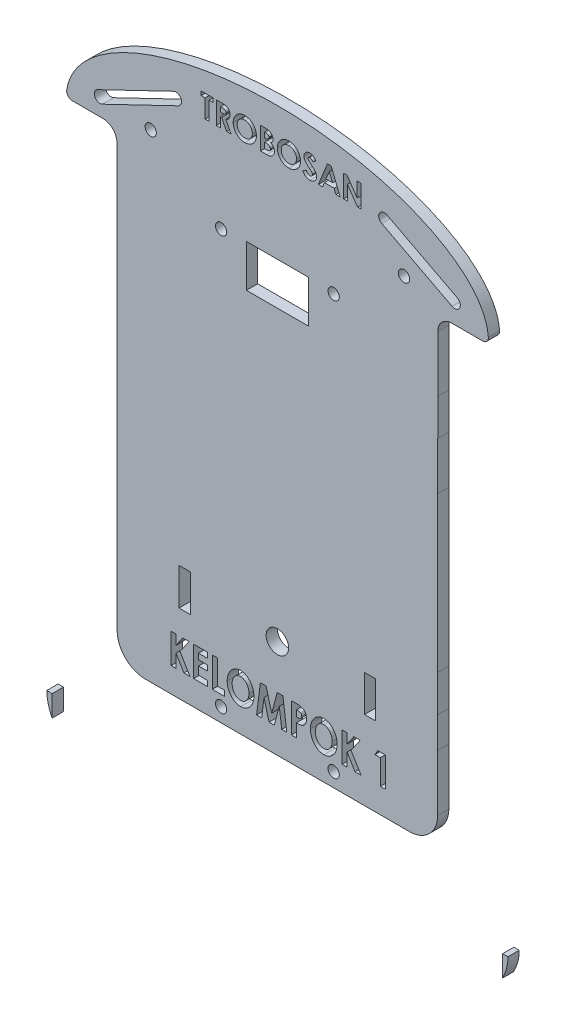
SolidWorks part; units mm, degrees
ref_plane "Front Plane" through (0, 0, 0) normal (0, 0, 1) x (1, 0, 0)
ref_plane "Top Plane" through (0, 0, 0) normal (0, 1, 0) x (1, 0, 0)
ref_plane "Right Plane" through (0, 0, 0) normal (1, 0, 0) x (0, 0, -1)
sketch "Sketch1" plane through (0, 0, 0) normal (0, 0, 1) x (1, 0, 0)
  line L0 (50.4961, 0) -> (-50.4961, 0) construction
  line L1 (0, 94) -> (0, -94) construction
  line L2 (-57, 93) -> (-57, 43.7851)
  line L3 (-56.98, 18) -> (-56.97, 18)
  line L4 (-56.97, 18) -> (-56.97, -18)
  line L5 (-56.97, -18) -> (-56.96, -18)
  line L6 (-56.96, -18) -> (-56.96, -31)
  line L8 (56.96, -18) -> (56.96, -31)
  line L9 (56.96, -18) -> (56.97, -18)
  line L10 (56.97, -18) -> (56.97, 37)
  line L11 (56.97, 37) -> (56.98, 37)
  line L12 (57, 92) -> (57, 67)
  line L13 (0, 94) -> (0, 138.6441) construction
  line L14 (-75, 93) -> (-57, 93)
  line L15 (57, 92) -> (74.9694, 92)
  line L16 (-81.94, -93) -> (-56.94, -93)
  line L17 (56.94, -93) -> (81.94, -93)
  line L18 (-57, 43.7851) -> (-56.99, 43.8393)
  line L19 (-56.99, 43.8393) -> (-56.99, 35)
  line L20 (-56.99, 35) -> (-56.98, 35)
  line L21 (-56.98, 35) -> (-56.98, 18)
  line L22 (57, 67) -> (56.99, 67)
  line L23 (56.99, 67) -> (56.99, 54)
  line L24 (56.99, 54) -> (56.98, 54)
  line L25 (56.98, 54) -> (56.98, 37)
  line L26 (-56.96, -31) -> (-56.95, -31)
  line L27 (-56.95, -42) -> (-56.94, -42)
  line L28 (-56.94, -42) -> (-56.94, -93)
  line L29 (-56.95, -31) -> (-56.95, -42)
  line L30 (-56.94, -93) -> (56.94, -93) construction
  line L31 (56.96, -31) -> (56.95, -31)
  line L32 (56.95, -31) -> (56.95, -42)
  line L33 (56.95, -42) -> (56.94, -42)
  line L34 (56.94, -42) -> (56.94, -93)
  circle A2 centre (0, 94) radius 10
  circle A3 centre (0, -94) radius 10
  circle A4 centre (0, 0) radius 1.9726
  ellipse E0 centre (0, 93) end of major axis (-75, 93) minor radius 35 (-75, 93) -> (74.9694, 92) cw
  ellipse E1 centre (0, -93) end of major axis (81.94, -93) minor radius 35 (-81.94, -93) -> (81.94, -93) ccw
  point P4 (0, 0)
  point P8 (0, 0)
  point P39 (0, -128)
  point P53 (-57, 93)
extrude "Boss-Extrude2" add sketch "Sketch1" along normal blind 4
sketch "Sketch25" plane through (0, 0, 0) normal (0, 0, -1) x (-1, 0, 0)
  line L1 (-30.9594, 48) -> (-30.9594, 34.3965) construction
  line L5 (-30.9594, 48) -> (-25.9623, 48)
  line L6 (-30.9594, 48) -> (-30.9594, 35.0074)
  line L7 (-30.9594, 35.0074) -> (-25.9623, 35.0074)
  line L8 (-25.9623, 48) -> (-25.9623, 35.0074)
  line L12 (25.0086, 48) -> (30.0057, 48)
  line L13 (25.0086, 48) -> (25.0086, 35.0074)
  line L14 (25.0086, 35.0074) -> (30.0057, 35.0074)
  line L15 (30.0057, 48) -> (30.0057, 35.0074)
  line L22 (-39.9543, -30.9549) -> (-34.9572, -30.9549)
  line L23 (-39.9543, -30.9549) -> (-39.9543, -43.9474)
  line L24 (-39.9543, -43.9474) -> (-34.9572, -43.9474)
  line L25 (-34.9572, -30.9549) -> (-34.9572, -43.9474)
  line L26 (35.0029, -30.9549) -> (40, -30.9549)
  line L27 (35.0029, -30.9549) -> (35.0029, -43.9474)
  line L28 (35.0029, -43.9474) -> (40, -43.9474)
  line L29 (40, -30.9549) -> (40, -43.9474)
  dimension "D2" = 4.9971
  dimension "D5" = 4.9971
  dimension "D7" = 4.9971
  dimension "D8" = 4.9971
extrude "Cut-Extrude25" cut sketch "Sketch25" against normal through all
sketch "Sketch28" plane through (0, 0, 0) normal (0, 0, -1) x (-1, 0, 0)
  line L1 (30, -112) -> (-30, -112)
  line L2 (-30, 112) -> (30, 112) construction
  line L3 (-30, 114) -> (30, 114)
  line L4 (-30, 110) -> (30, 110)
  line L5 (-30, -112) -> (30, -112) construction
  line L6 (-30, -110) -> (30, -110)
  line L7 (-30, -114) -> (30, -114)
  line L8 (-63, 99) -> (-38, 112) construction
  line L9 (-63.9227, 100.7744) -> (-38.9227, 113.7744)
  line L10 (-62.0773, 97.2256) -> (-37.0773, 110.2256)
  line L11 (36.0632, 112.09) -> (63.0485, 99.1007) construction
  line L12 (36.9306, 113.8921) -> (63.9159, 100.9028)
  line L13 (35.1957, 110.2879) -> (62.1811, 97.2986)
  line L21 (36, -112) -> (63, -99) construction
  line L22 (35.1324, -110.198) -> (62.1324, -97.198)
  line L23 (36.8676, -113.802) -> (63.8676, -100.802)
  line L24 (-63, -99) -> (-38, -112.1208) construction
  line L25 (-62.0706, -97.2291) -> (-37.0706, -110.3499)
  line L26 (-63.9294, -100.7709) -> (-38.9294, -113.8918)
  arc A0 (-30, 114) -> (-30, 110) centre (-30, 112) ccw
  arc A1 (30, 110) -> (30, 114) centre (30, 112) ccw
  arc A2 (-63.9227, 100.7744) -> (-62.0773, 97.2256) centre (-63, 99) ccw
  arc A4 (-37.0773, 110.2256) -> (-38.9227, 113.7744) centre (-38, 112) ccw
  arc A5 (36.9306, 113.8921) -> (35.1957, 110.2879) centre (36.0632, 112.09) ccw
  arc A6 (62.1811, 97.2986) -> (63.9159, 100.9028) centre (63.0485, 99.1007) ccw
  arc A7 (35.1324, -110.198) -> (36.8676, -113.802) centre (36, -112) ccw
  arc A8 (-30, -110) -> (-30, -114) centre (-30, -112) ccw
  arc A9 (30, -114) -> (30, -110) centre (30, -112) ccw
  arc A11 (63.8676, -100.802) -> (62.1324, -97.198) centre (63, -99) ccw
  arc A12 (-62.0706, -97.2291) -> (-63.9294, -100.7709) centre (-63, -99) ccw
  arc A13 (-38.9294, -113.8918) -> (-37.0706, -110.3499) centre (-38, -112.1208) ccw
  point P4 (0, -112)
  point P6 (0, -112)
  point P10 (0, 112)
  point P15 (-36, -112)
  point P16 (0, -112)
  point P22 (-30, -112)
  point P23 (-38, -112.1208)
  point P25 (63.0485, 99.1007)
  point P26 (-38, 112)
  point P29 (-50.5, 105.5)
  point P35 (34, -112)
  point P36 (36.0632, 112.09)
  point P39 (49.5558, 105.5954)
  point P44 (30, -112)
  point P57 (36, -112)
  point P60 (49.5, -105.5)
  point P65 (-50.5, -105.5604)
extrude "Cut-Extrude29" cut sketch "Sketch28" against normal through all contours L9 A4 L10 A2 | L3 A1 L4 A0 | L12 A6 L13 A5 | L26 A13 L25 A12 | L7 A9 L6 A8 | L23 A11 L22 A7
sketch "Sketch33" plane through (0, 0, 0) normal (0, 0, -1) x (-1, 0, 0)
  line L1 (-12.8608, 105.0896) -> (12.8076, 105.0896)
  line L2 (-12.8608, 105.0896) -> (-12.8608, 83.2737)
  line L3 (-12.8608, 83.2737) -> (12.8076, 83.2737)
  line L4 (12.8076, 105.0896) -> (12.8076, 83.2737)
extrude "Boss-Extrude6" add sketch "Sketch33" against normal blind 4
sketch "Sketch34" plane through (0, 0, 4) normal (0, 0, 1) x (1, 0, 0)
  line L1 (-50, 50) -> (50, 50)
  line L2 (-50, 50) -> (-50, 34.3734)
  line L3 (-50, 34.3734) -> (50, 34.3734)
  line L4 (50, 50) -> (50, 34.3734)
extrude "Boss-Extrude8" add sketch "Sketch34" against normal blind 4
sketch "Sketch35" plane through (0, 0, 4) normal (0, 0, 1) x (1, 0, 0)
  line L1 (-4.2047, 3.8705) -> (3.3615, 3.8705)
  line L2 (-4.2047, 3.8705) -> (-4.2047, -3.8104)
  line L3 (-4.2047, -3.8104) -> (3.3615, -3.8104)
  line L4 (3.3615, 3.8705) -> (3.3615, -3.8104)
extrude "Boss-Extrude9" add sketch "Sketch35" against normal blind 4
sketch "Sketch42" plane through (0, 0, 4) normal (0, 0, 1) x (1, 0, 0)
  line L1 (-33.2628, 115.9037) -> (33.3138, 115.9037)
  line L2 (-33.2628, 115.9037) -> (-33.2628, 108.319)
  line L3 (-33.2628, 108.319) -> (33.3138, 108.319)
  line L4 (33.3138, 115.9037) -> (33.3138, 108.319)
extrude "Boss-Extrude12" add sketch "Sketch42" against normal blind 4
sketch "Sketch43" plane through (0, 0, 4) normal (0, 0, 1) x (1, 0, 0)
  line L1 (-80.0131, -72) -> (80.041, -72)
  line L2 (-80.0131, -72) -> (-80.0131, -132.0859)
  line L3 (-80.0131, -132.0859) -> (80.041, -132.0859)
  line L4 (80.041, -72) -> (80.041, -132.0859)
extrude "Cut-Extrude33" cut sketch "Sketch43" against normal blind 4
fillet "Fillet2" radius 10 1 edges at (56.94, -72, 2)
fillet "Fillet3" radius 10 1 edges at (-56.94, -72, 2)
sketch "Sketch45" plane through (0, 0, 4) normal (0, 0, 1) x (1, 0, 0)
  text T0 "TROBOSAN" font "Century Gothic" height in points 30
extrude "Cut-Extrude34" cut sketch "Sketch45" against normal blind 4
sketch "Sketch48" plane through (0, 0, 4) normal (0, 0, 1) x (1, 0, 0)
  line L1 (-31.0624, 77.2289) -> (-30.1532, 77.2289)
  line L2 (-31.0624, 77.2289) -> (-31.0624, 89.114)
  line L3 (-31.0624, 89.114) -> (-30.1532, 89.114)
  line L4 (-30.1532, 77.2289) -> (-30.1532, 89.114)
extrude "Boss-Extrude23" add sketch "Sketch48" against normal blind 4
sketch "Sketch55" plane through (0, 0, 4) normal (0, 0, 1) x (1, 0, 0)
  line L1 (-9.1573, 105.5891) -> (-8.1537, 105.5891)
  line L2 (-9.1573, 105.5891) -> (-9.1573, 94.169)
  line L3 (-9.1573, 94.169) -> (-8.1537, 94.169)
  line L4 (-8.1537, 105.5891) -> (-8.1537, 94.169)
extrude "Boss-Extrude24" add sketch "Sketch55" against normal blind 4
sketch "Sketch56" plane through (0, 0, 4) normal (0, 0, 1) x (1, 0, 0)
  line L1 (-19.2633, 76.1985) -> (-18.0661, 76.1985)
  line L2 (-19.2633, 76.1985) -> (-19.2633, 63.6372)
  line L3 (-19.2633, 63.6372) -> (-18.0661, 63.6372)
  line L4 (-18.0661, 76.1985) -> (-18.0661, 63.6372)
extrude "Boss-Extrude25" add sketch "Sketch56" against normal blind 4
sketch "Sketch57" plane through (0, 0, 4) normal (0, 0, 1) x (1, 0, 0)
  line L1 (2.6551, 104.706) -> (3.8655, 104.706)
  line L2 (2.6551, 104.706) -> (2.6551, 91.4382)
  line L3 (2.6551, 91.4382) -> (3.8655, 91.4382)
  line L4 (3.8655, 104.706) -> (3.8655, 91.4382)
extrude "Boss-Extrude26" add sketch "Sketch57" against normal blind 4
sketch "Sketch62" plane through (0, 0, 4) normal (0, 0, 1) x (1, 0, 0)
  line L0 (19.7899, 94.7418) -> (24.1136, 106.2108)
extrude "Extrude-Thin6" add sketch "Sketch62" against normal blind 4 thin thin type one direction wall 1
sketch "Sketch63" plane through (0, 0, 4) normal (0, 0, 1) x (1, 0, 0)
  circle A0 centre (20, 80) radius 2
extrude "Cut-Extrude35" cut sketch "Sketch63" against normal blind 4
sketch "Sketch64" plane through (0, 0, 4) normal (0, 0, 1) x (1, 0, 0)
  circle A0 centre (-20, 80) radius 2
extrude "Cut-Extrude36" cut sketch "Sketch64" against normal blind 4
fillet "Fillet4" radius 5 1 edges at (-57, 93, 2)
fillet "Fillet5" radius 5 1 edges at (57, 92, 2)
fillet "Fillet6" radius 2 3 edges at (1.0715, 127.9964, 0) (74.9694, 92, 2) (1.0715, 127.9964, 4)
fillet "Fillet7" radius 2 1 edges at (-75, 93, 2)
sketch "Sketch65" plane through (0, 0, 4) normal (0, 0, 1) x (1, 0, 0)
  text T0 "KELOMPOK 1" font "Century Gothic" height in points 40
extrude "Cut-Extrude37" cut sketch "Sketch65" against normal blind 10
sketch "Sketch66" plane through (0, 0, 4) normal (0, 0, 1) x (1, 0, 0)
  circle A0 centre (-45, 98) radius 2
extrude "Cut-Extrude38" cut sketch "Sketch66" against normal blind 10
sketch "Sketch67" plane through (0, 0, 4) normal (0, 0, 1) x (1, 0, 0)
  circle A0 centre (45, 98) radius 2
extrude "Cut-Extrude39" cut sketch "Sketch67" against normal blind 10
sketch "Sketch68" plane through (0, 0, 4) normal (0, 0, 1) x (1, 0, 0)
  circle A0 centre (-20, -67) radius 2
extrude "Cut-Extrude40" cut sketch "Sketch68" against normal blind 10
sketch "Sketch69" plane through (0, 0, 4) normal (0, 0, 1) x (1, 0, 0)
  circle A0 centre (20, -67) radius 2
extrude "Cut-Extrude41" cut sketch "Sketch69" against normal blind 10
sketch "Sketch70" plane through (0, 0, 4) normal (0, 0, 1) x (1, 0, 0)
  line L1 (-13.5939, -66.7195) -> (-12.6198, -66.7195)
  line L2 (-13.5939, -66.7195) -> (-13.5939, -64.6507)
  line L3 (-13.5939, -64.6507) -> (-12.6198, -64.6507)
  line L4 (-12.6198, -66.7195) -> (-12.6198, -64.6507)
extrude "Boss-Extrude27" add sketch "Sketch70" against normal blind 4
sketch "Sketch71" plane through (0, 0, 4) normal (0, 0, 1) x (1, 0, 0)
  line L1 (2.4897, -65.6162) -> (7.4437, -65.6162)
  line L2 (2.4897, -65.6162) -> (2.4897, -66.3931)
  line L3 (2.4897, -66.3931) -> (7.4437, -66.3931)
  line L4 (7.4437, -65.6162) -> (7.4437, -66.3931)
extrude "Boss-Extrude28" add sketch "Sketch71" against normal blind 4
sketch "Sketch72" plane through (0, 0, 4) normal (0, 0, 1) x (1, 0, 0)
  line L1 (16.1568, -67.0347) -> (16.3616, -67.0347)
  line L2 (16.1568, -67.0347) -> (16.1568, -69.5523)
  line L3 (16.1568, -69.5523) -> (16.3616, -69.5523)
  line L4 (16.3616, -67.0347) -> (16.3616, -69.5523)
extrude "Boss-Extrude29" add sketch "Sketch72" against normal blind 4
sketch "Sketch73" plane through (0, 0, 4) normal (0, 0, 1) x (1, 0, 0)
  line L1 (-22.8107, 82.4736) -> (22.9836, 82.4736)
  line L2 (-22.8107, 82.4736) -> (-22.8107, 77.0349)
  line L3 (-22.8107, 77.0349) -> (22.9836, 77.0349)
  line L4 (22.9836, 82.4736) -> (22.9836, 77.0349)
extrude "Boss-Extrude30" add sketch "Sketch73" against normal blind 4
sketch "Sketch74" plane through (0, 0, 4) normal (0, 0, 1) x (1, 0, 0)
  line L1 (-41.7838, -30.4049) -> (41.6123, -30.4049)
  line L2 (-41.7838, -30.4049) -> (-41.7838, -45.0406)
  line L3 (-41.7838, -45.0406) -> (41.6123, -45.0406)
  line L4 (41.6123, -30.4049) -> (41.6123, -45.0406)
extrude "Boss-Extrude31" add sketch "Sketch74" against normal blind 4
sketch "Sketch75" plane through (0, 0, 4) normal (0, 0, 1) x (1, 0, 0)
  line L0 (-57, 88) -> (-57, 43.7851) construction
  line L1 (-11, 80.647) -> (11, 80.647)
  line L2 (-11, 80.647) -> (-11, 65.6156)
  line L3 (-11, 65.6156) -> (11, 65.6156)
  line L4 (11, 80.647) -> (11, 65.6156)
  line L5 (57, 67) -> (57, 87) construction
  dimension "D1" = 46
  dimension "D2" = 46
extrude "Cut-Extrude42" cut sketch "Sketch75" against normal blind 4
sketch "Sketch76" plane through (0, 0, 4) normal (0, 0, 1) x (1, 0, 0)
  circle A0 centre (-20, 80) radius 2
extrude "Cut-Extrude43" cut sketch "Sketch76" against normal blind 10
sketch "Sketch77" plane through (0, 0, 4) normal (0, 0, 1) x (1, 0, 0)
  circle A0 centre (20, 80) radius 2
extrude "Cut-Extrude44" cut sketch "Sketch77" against normal blind 10
sketch "Sketch78" plane through (0, 0, 4) normal (0, 0, 1) x (1, 0, 0)
  line L1 (-34.9572, -31) -> (-30.95, -31)
  line L2 (-34.9572, -31) -> (-34.9572, -44.1451)
  line L3 (-34.9572, -44.1451) -> (-30.95, -44.1451)
  line L4 (-30.95, -31) -> (-30.95, -44.1451)
extrude "Cut-Extrude45" cut sketch "Sketch78" against normal blind 10
sketch "Sketch79" plane through (0, 0, 4) normal (0, 0, 1) x (1, 0, 0)
  line L1 (34.9572, -31) -> (30.95, -31)
  line L2 (34.9572, -31) -> (34.9572, -43.9474)
  line L3 (34.9572, -43.9474) -> (30.95, -43.9474)
  line L4 (30.95, -31) -> (30.95, -43.9474)
extrude "Cut-Extrude46" cut sketch "Sketch79" against normal blind 10
sketch "Sketch80" plane through (0, 0, 4) normal (0, 0, 1) x (1, 0, 0)
  circle A0 centre (0, -37) radius 4
extrude "Cut-Extrude47" cut sketch "Sketch80" against normal blind 10
equation "\"D1@Sketch75\"=46.0"
